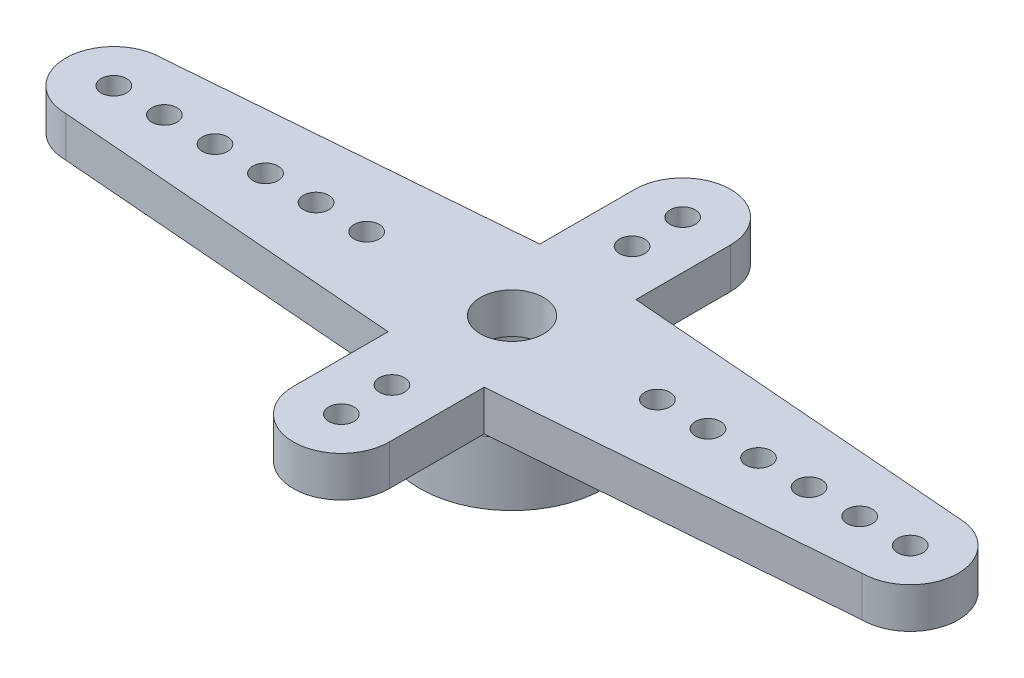
SolidWorks part; units mm, degrees
ref_plane "Front Plane" through (0, 0, 0) normal (0, 0, 1) x (1, 0, 0)
ref_plane "Top Plane" through (0, 0, 0) normal (0, 1, 0) x (1, 0, 0)
ref_plane "Right Plane" through (0, 0, 0) normal (1, 0, 0) x (0, 0, -1)
sketch "Sketch1" plane through (0, 0, 0) normal (0, 1, 0) x (1, 0, 0)
  circle A0 centre (0, 0) radius 2.5
  circle A1 centre (0, 0) radius 3.65
  dimension "D1" = 5
  dimension "D2" = 7.3
extrude "Boss-Extrude1" add sketch "Sketch1" along normal blind 2.5
sketch "Sketch2" plane through (0, 2.5, 0) normal (0, 1, 0) x (1, 0, 0)
  line L0 (15.75, 0) -> (-15.75, 0) construction
  line L1 (0, -6.75) -> (0, 6.75) construction
  line L2 (-1.9, 6.75) -> (-1.9, 3)
  line L3 (1.9, 6.75) -> (1.9, 3)
  line L4 (-15.75, 1.9) -> (-1.9, 3)
  line L5 (15.75, 1.9) -> (1.9, 3)
  line L6 (15.75, -1.9) -> (1.9, -3)
  line L7 (1.9, -6.75) -> (1.9, -3)
  line L8 (-1.9, -6.75) -> (-1.9, -3)
  line L9 (-15.75, -1.9) -> (-1.9, -3)
  circle A0 centre (0, 0) radius 1.25
  arc A1 (-1.9, 6.75) -> (1.9, 6.75) centre (0, 6.75) cw
  arc A2 (-15.75, 1.9) -> (-15.75, -1.9) centre (-15.75, 0) ccw
  arc A3 (15.75, 1.9) -> (15.75, -1.9) centre (15.75, 0) cw
  arc A4 (-1.9, -6.75) -> (1.9, -6.75) centre (0, -6.75) ccw
  point P6 (0, 0)
  point P9 (0, 0)
  dimension "D1" = 2.5
  dimension "D4" = 1.9
  dimension "D5" = 1.9
  dimension "D2" = 13.5
  dimension "D3" = 31.5
  dimension "D6" = 1.1
extrude "Boss-Extrude2" add sketch "Sketch2" along normal blind 1.6
sketch "Sketch3" plane through (0, 4.1, 0) normal (0, 1, 0) x (1, 0, 0)
  line L0 (0, -8.65) -> (0, 8.65) construction
  line L1 (-17.65, 0) -> (17.65, 0) construction
  arc A0 (1.9, 6.75) -> (-1.9, 6.75) centre (0, 6.75) ccw construction
  arc A1 (15.75, -1.9) -> (15.75, 1.9) centre (15.75, 0) ccw construction
  circle A2 centre (0, 6.75) radius 0.5
  circle A3 centre (0, 4.75) radius 0.5
  circle A4 centre (-15.75, 0) radius 0.5
  circle A5 centre (-13.75, 0) radius 0.5
  circle A6 centre (-11.75, 0) radius 0.5
  circle A7 centre (-9.75, 0) radius 0.5
  circle A8 centre (-7.75, 0) radius 0.5
  circle A9 centre (-5.75, 0) radius 0.5
  circle A10 centre (5.75, 0) radius 0.5
  circle A11 centre (7.75, 0) radius 0.5
  circle A12 centre (9.75, 0) radius 0.5
  circle A13 centre (11.75, 0) radius 0.5
  circle A14 centre (13.75, 0) radius 0.5
  circle A15 centre (15.75, 0) radius 0.5
  circle A16 centre (0, -4.75) radius 0.5
  circle A17 centre (0, -6.75) radius 0.5
  point P8 (0, 0)
  point P15 (0, 0)
  point P44 (0, 0)
  dimension "D1" = 1
  dimension "D3" = 1
  dimension "D4" = 1
  dimension "D5" = 2
  dimension "D2" = 6
extrude "Cut-Extrude1" cut sketch "Sketch3" against normal up to next
